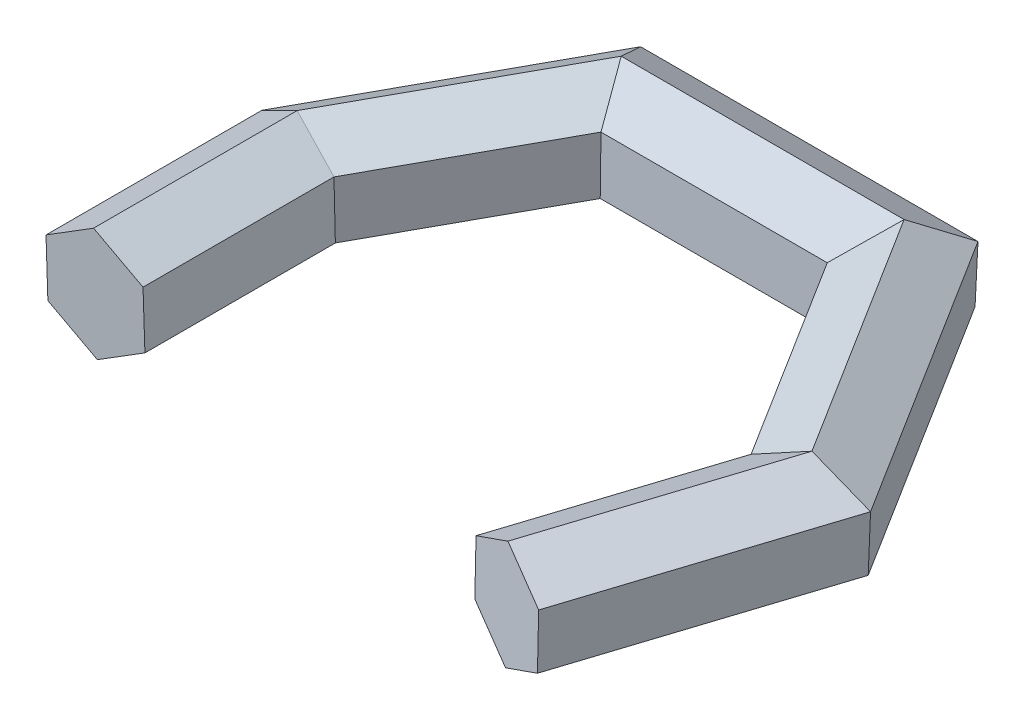
SolidWorks part; units mm, degrees
ref_plane "Front Plane" through (0, 0, 0) normal (0, 0, 1) x (1, 0, 0)
ref_plane "Top Plane" through (0, 0, 0) normal (0, 1, 0) x (1, 0, 0)
ref_plane "Right Plane" through (0, 0, 0) normal (1, 0, 0) x (0, 0, -1)
sketch "Sketch1" plane through (0, 0, 0) normal (0, 0, 1) x (1, 0, 0)
  line L2 (8.8241, -4.7049) -> (8.4866, 5.2894)
  line L3 (8.4866, 5.2894) -> (-0.3375, 9.9943)
  line L4 (-0.3375, 9.9943) -> (-8.8241, 4.7049)
  line L5 (-8.8241, 4.7049) -> (-8.4866, -5.2894)
  line L6 (-8.4866, -5.2894) -> (0.3375, -9.9943)
  line L7 (0.3375, -9.9943) -> (8.8241, -4.7049)
  circle A1 centre (0, 0) radius 8.6603 construction
sketch "Sketch3" plane through (0, 0, 0) normal (0, 1, 0) x (1, 0, 0)
  line L0 (0, 0) -> (0, 36.2422)
  line L1 (0, 36.2422) -> (20.3608, 73.2988)
  line L2 (20.3608, 73.2988) -> (70.4483, 73.2988)
  line L3 (70.4483, 73.2988) -> (97.837, 29.5822)
  line L4 (97.837, 29.5822) -> (84.6728, -11.2964)
  point P3 (0, 39.4999)
  point P8 (27.6907, 58.2318)
  point P9 (65.5617, 43.9793)
  point P10 (79.407, 3.6649)
  point P11 (54.1597, -30.134)
  point P12 (0, 0)
  point P13 (0, 0)
  point P14 (92.0307, 33.3917)
  point P15 (63.5256, 71.2627)
  point P16 (6.5154, 71.2627)
  point P17 (63.1184, 85.5153)
  point P18 (91.6235, 39.4999)
  point P19 (76.1493, -8.5515)
  point P20 (0, 39.4999)
  point P21 (0, 39.4999)
  point P22 (0, 0)
  point P23 (0, 0)
  point P24 (0, 0)
  point P25 (0, 0)
  point P26 (0, 0)
  point P27 (0, 36.2422)
  point P28 (20.3608, 73.2988)
  point P29 (70.4483, 73.2988)
sweep "Sweep2" add profiles "Sketch1" path "Sketch3"
